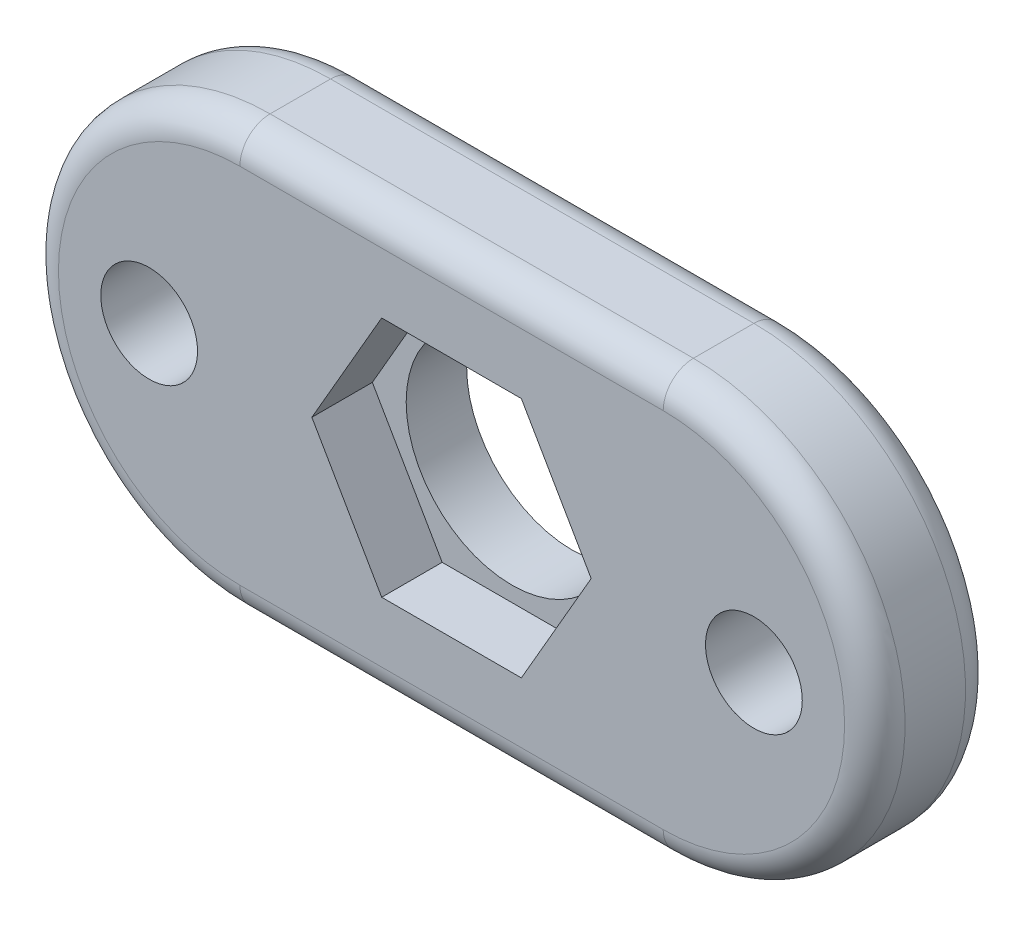
SolidWorks part; units mm, degrees
ref_plane "Plan de face" through (0, 0, 0) normal (0, 0, 1) x (1, 0, 0)
ref_plane "Plan de dessus" through (0, 0, 0) normal (0, 1, 0) x (1, 0, 0)
ref_plane "Plan de droite" through (0, 0, 0) normal (1, 0, 0) x (0, 0, -1)
sketch "Esquisse1" plane through (0, 0, 0) normal (0, 0, 1) x (1, 0, 0)
  line L0 (-27.2542, 0) -> (-13.2542, 0) construction
  line L1 (-27.2542, 7) -> (-13.2542, 7)
  line L2 (-27.2542, -7) -> (-13.2542, -7)
  arc A0 (-27.2542, 7) -> (-27.2542, -7) centre (-27.2542, 0) ccw
  arc A1 (-13.2542, -7) -> (-13.2542, 7) centre (-13.2542, 0) ccw
  point P3 (-20.2542, 0)
  dimension "D1" = 14
  dimension "D2" = 14
extrude "Boss.-Extru.1" add sketch "Esquisse1" along normal blind 4
sketch "Esquisse3" plane through (0, 0, 4) normal (0, 0, 1) x (1, 0, 0)
  line L0 (-27.2542, -7) -> (-13.2542, -7) construction
  circle A0 centre (-20.2542, 0) radius 3.5
  circle A1 centre (-30.2542, 0) radius 1.6
  circle A2 centre (-10.2542, 0) radius 1.6
  dimension "D1" = 3.2
  dimension "D2" = 3.2
  dimension "D5" = 7
  dimension "D3" = 20
  dimension "D4" = 10
  dimension "D6" = 7
  dimension "D7" = 7
  dimension "D8" = 7
  dimension "D9" = 7
extrude "Enlèv. mat.-Extru.1" cut sketch "Esquisse3" against normal through all
sketch "Esquisse4" plane through (0, 0, 4) normal (0, 0, 1) x (1, 0, 0)
  line L0 (-13.2542, 7) -> (-27.2542, 7) construction
  line L1 (-22.5636, 4) -> (-24.873, 0)
  line L2 (-24.873, 0) -> (-22.5636, -4)
  line L3 (-22.5636, -4) -> (-17.9448, -4)
  line L4 (-17.9448, -4) -> (-15.6354, 0)
  line L5 (-15.6354, 0) -> (-17.9448, 4)
  line L6 (-17.9448, 4) -> (-22.5636, 4)
  circle A0 centre (-20.2542, 0) radius 4 construction
  dimension "D1" = 8
extrude "Enlèv. mat.-Extru.2" cut sketch "Esquisse4" against normal blind 2
fillet "Congé1" radius 1 8 edges at (-20.2542, 7, 4) (-6.2542, 0, 4) (-20.2542, -7, 4) (-20.2542, 7, 0) (-6.2542, 0, 0) (-20.2542, -7, 0) (-34.2542, 0, 4) (-34.2542, 0, 0)
